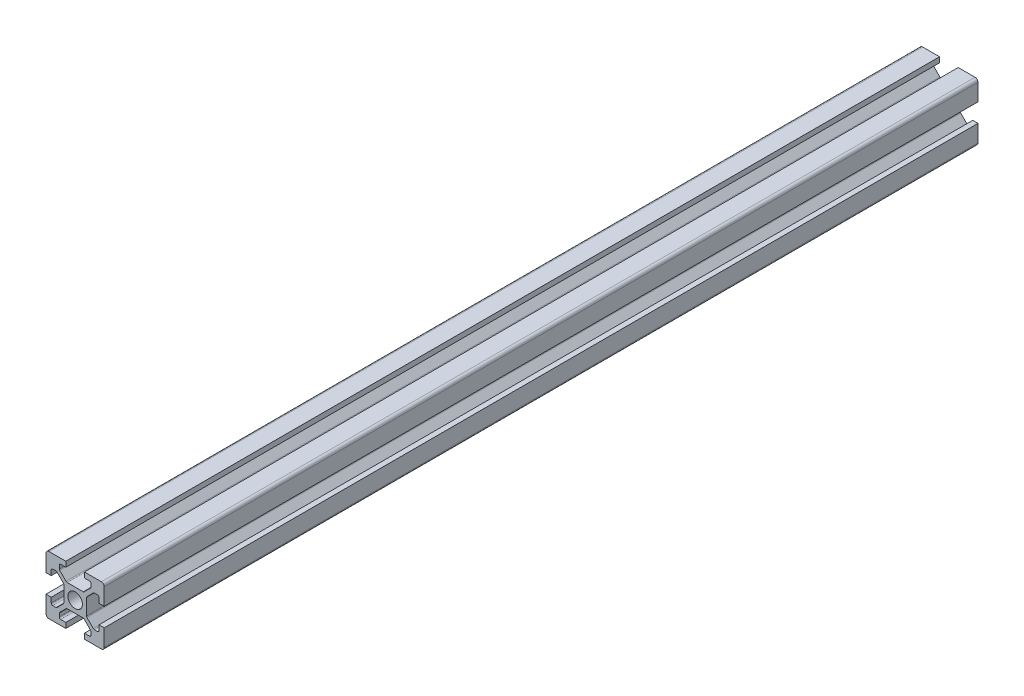
SolidWorks part; units mm, degrees
material "1060 Alloy"
ref_plane "Front Plane" through (0, 0, 0) normal (0, 0, 1) x (1, 0, 0)
ref_plane "Top Plane" through (0, 0, 0) normal (0, 1, 0) x (1, 0, 0)
ref_plane "Right Plane" through (0, 0, 0) normal (1, 0, 0) x (0, 0, -1)
sketch "Sketch1" plane through (0, 0, 0) normal (0, 0, 1) x (1, 0, 0)
  line L0 (20, 0) -> (-8.059, 28.059) construction
  line L1 (0, 0) -> (6.8, 0)
  line L2 (0, 0) -> (0, 6.8)
  line L3 (0, 20) -> (6.8, 20)
  line L4 (20, 0) -> (20, 6.8)
  line L5 (6.8, 20) -> (6.8, 18.2)
  line L6 (20, 20) -> (8.2322, 8.2322) construction
  line L7 (12.95, 6.1) -> (7.05, 6.1)
  line L8 (13.9, 7.05) -> (13.9, 12.95)
  line L9 (12.95, 13.9) -> (7.05, 13.9)
  line L10 (6.1, 7.05) -> (6.1, 12.95)
  line L11 (13.9, 6.1) -> (6.1, 13.9) construction
  line L12 (13.9, 13.9) -> (6.1, 6.1) construction
  line L13 (4.55, 16.4) -> (7.05, 13.9)
  line L14 (13.2, 18.2) -> (13.2, 20)
  line L15 (1.8, 6.8) -> (0, 6.8)
  line L16 (0, 13.2) -> (0, 20)
  line L17 (0, 13.2) -> (1.8, 13.2)
  line L18 (10, 10) -> (10, 13.9) construction
  line L19 (16.4, 4.55) -> (13.9, 7.05)
  line L20 (4.55, 16.4) -> (4.55, 18.2)
  line L21 (4.55, 18.2) -> (6.8, 18.2)
  line L22 (13.2, 18.2) -> (15.45, 18.2)
  line L23 (15.45, 18.2) -> (15.45, 16.4)
  line L24 (15.45, 16.4) -> (12.95, 13.9)
  line L25 (16.4, 4.55) -> (18.2, 4.55)
  line L26 (18.2, 4.55) -> (18.2, 6.8)
  line L27 (20, 6.8) -> (18.2, 6.8)
  line L28 (18.2, 13.2) -> (20, 13.2)
  line L29 (18.2, 13.2) -> (18.2, 15.45)
  line L30 (18.2, 15.45) -> (16.4, 15.45)
  line L31 (16.4, 15.45) -> (13.9, 12.95)
  line L32 (1.8, 4.55) -> (3.6, 4.55)
  line L33 (3.6, 15.45) -> (6.1, 12.95)
  line L34 (3.6, 15.45) -> (1.8, 15.45)
  line L35 (1.8, 15.45) -> (1.8, 13.2)
  line L36 (0, 13.2) -> (1.8, 13.2)
  line L37 (1.8, 6.8) -> (0, 6.8)
  line L38 (3.6, 4.55) -> (6.1, 7.05)
  line L39 (1.8, 6.8) -> (1.8, 4.55)
  line L40 (15.45, 3.6) -> (12.95, 6.1)
  line L41 (4.55, 3.6) -> (7.05, 6.1)
  line L42 (4.55, 1.8) -> (4.55, 3.6)
  line L43 (6.8, 1.8) -> (4.55, 1.8)
  line L44 (6.8, 1.8) -> (6.8, 0)
  line L45 (15.45, 3.6) -> (15.45, 1.8)
  line L46 (15.45, 1.8) -> (13.2, 1.8)
  line L47 (13.2, 0) -> (13.2, 1.8)
  line L48 (13.2, 20) -> (20, 20)
  line L49 (20, 13.2) -> (20, 20)
  line L50 (13.2, 0) -> (20, 0)
  line L51 (6.1, 6.1) -> (-5.5045, -5.5045) construction
  circle A0 centre (10, 10) radius 2.5
  point P23 (-11.0197, 11.202)
  point P25 (10, 16.4)
  point P39 (13.2, 19.1)
  point P46 (0.9, 6.8)
  point P58 (-7.027, 8.7292)
  dimension "D3" = 5
  dimension "D2" = 20
  dimension "D4" = 7.8
  dimension "D5" = 7.8
  dimension "D6" = 6.8
  dimension "D7" = 6.8
  dimension "D8" = 1.8
  dimension "D9" = 10.9
  dimension "D10" = 1.8
  dimension "D11" = 10.9
  dimension "D12" = 20
extrude "Boss-Extrude1" add sketch "Sketch1" along normal blind 300 contours L47 L50 L4 L27 L26 L25 L19 L8 L31 L30 L29 L28 L49 L48 L14 L22 L23 L24 L9 L13 L20 L21 L5 L3 L16 L17 L35 L34 L33 L10 L38 L32 L39 L15 L2 L1 L44 L43 L42 L41 L7 L40 L45 L46 A0
fillet "Fillet1" radius 1 4 edges at (20, 20, 150) (20, 0, 150) (0, 0, 150) (0, 20, 150)
fillet "Fillet2" radius 0.5 6 edges at (4.55, 18.2, 150) (4.55, 16.4, 150) (7.05, 13.9, 150) (15.45, 18.2, 150) (15.45, 16.4, 150) (12.95, 13.9, 150)
fillet "Fillet3" radius 0.5 6 edges at (18.2, 15.45, 150) (16.4, 15.45, 150) (13.9, 12.95, 150) (18.2, 4.55, 150) (13.9, 7.05, 150) (16.4, 4.55, 150)
fillet "Fillet4" radius 0.5 6 edges at (1.8, 15.45, 150) (3.6, 15.45, 150) (6.1, 12.95, 150) (3.6, 4.55, 150) (1.8, 4.55, 150) (6.1, 7.05, 150)
fillet "Fillet5" radius 0.5 6 edges at (7.05, 6.1, 150) (4.55, 3.6, 150) (4.55, 1.8, 150) (15.45, 1.8, 150) (15.45, 3.6, 150) (12.95, 6.1, 150)
